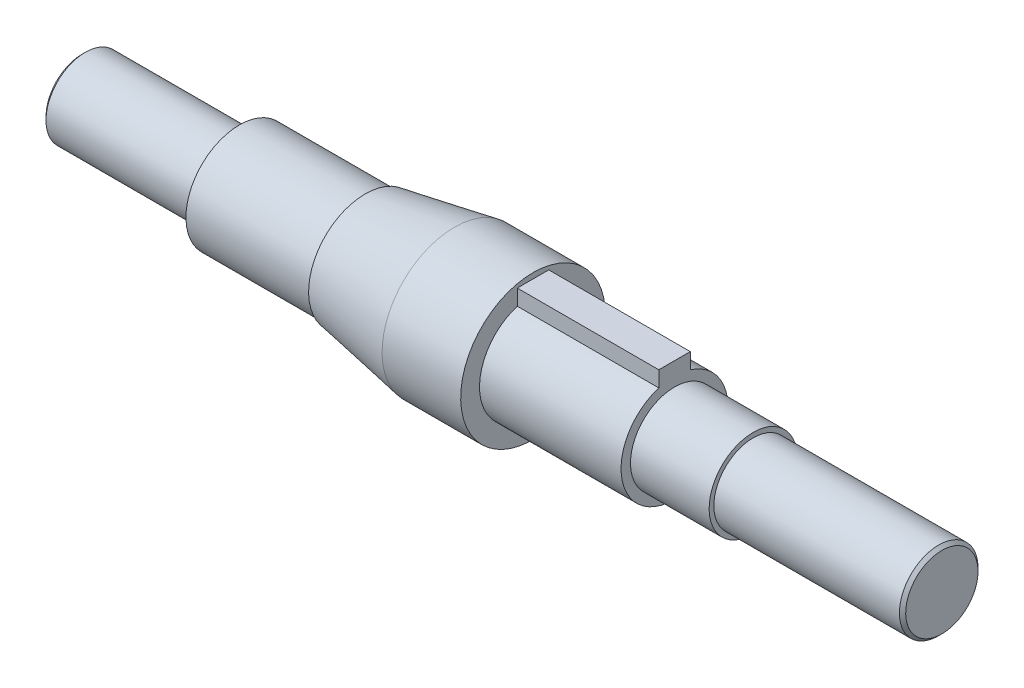
SolidWorks part; units mm, degrees
material "Plain Carbon Steel"
ref_plane "Front Plane" through (0, 0, 0) normal (0, 0, 1) x (1, 0, 0)
ref_plane "Top Plane" through (0, 0, 0) normal (0, 1, 0) x (1, 0, 0)
ref_plane "Right Plane" through (0, 0, 0) normal (1, 0, 0) x (0, 0, -1)
sketch "Sketch1" plane through (0, 0, 0) normal (0, 0, 1) x (1, 0, 0)
  line L0 (-136.6782, 12.5) -> (-86.6782, 12.5)
  line L1 (-86.6782, 12.5) -> (-86.6782, 17)
  line L2 (-86.6782, 17) -> (-46.6782, 17)
  line L3 (-46.6782, 17) -> (-46.6782, 18)
  line L4 (-46.6782, 18) -> (-18.3218, 23)
  line L5 (-18.3218, 23) -> (6.6782, 23)
  line L6 (6.6782, 23) -> (6.6782, 17)
  line L7 (6.6782, 17) -> (51.6782, 17)
  line L8 (51.6782, 17) -> (51.6782, 14)
  line L9 (51.6782, 14) -> (76.6782, 14)
  line L10 (76.6782, 14) -> (76.6782, 12.5)
  line L11 (76.6782, 12.5) -> (136.6782, 12.5)
  line L12 (136.6782, 12.5) -> (136.6782, 0)
  line L13 (136.6782, 0) -> (-136.6782, 0)
  line L14 (-136.6782, 0) -> (-136.6782, 12.5)
  point P2 (-66.6782, 17)
  point P16 (0, 0)
  point P18 (13.2538, 14)
  point P19 (0, 0)
  point P20 (0, 0)
  dimension "D1" = 12.5
  dimension "D2" = 50
  dimension "D3" = 17
  dimension "D4" = 17
  dimension "D5" = 12.5
  dimension "D6" = 14
  dimension "D7" = 25
  dimension "D8" = 23
  dimension "D9" = 45
  dimension "D10" = 25
  dimension "D11" = 60
  dimension "D12" = 18
  dimension "D13" = 10
  dimension "D14" = 40
revolve "Revolve1" add sketch "Sketch1" angle 360 about L13
sketch "Sketch3" plane through (51.6782, 0, 0) normal (1, 0, 0) x (0, 0, -1)
  line L0 (-5, 21.2481) -> (5, 21.2481)
  line L1 (5, 21.2481) -> (5, 16.2481)
  line L2 (-5, 21.2481) -> (-5, 16.2481)
  line L3 (0, 0) -> (0, 21.2481) construction
  line L4 (-5, 16.2481) -> (5, 16.2481)
  circle A0 centre (0, 0) radius 17 construction
  circle A1 centre (0, 0) radius 17 construction
  dimension "D1" = 5
  dimension "D2" = 10
extrude "Boss-Extrude1" add sketch "Sketch3" against normal up to surface (45 mm away) up to face at (6.6782, 23, 0)
chamfer "Chamfer1" distance 1 angle 45 2 edges at (136.6782, 12.5, 0) (-136.6782, 12.5, 0)
